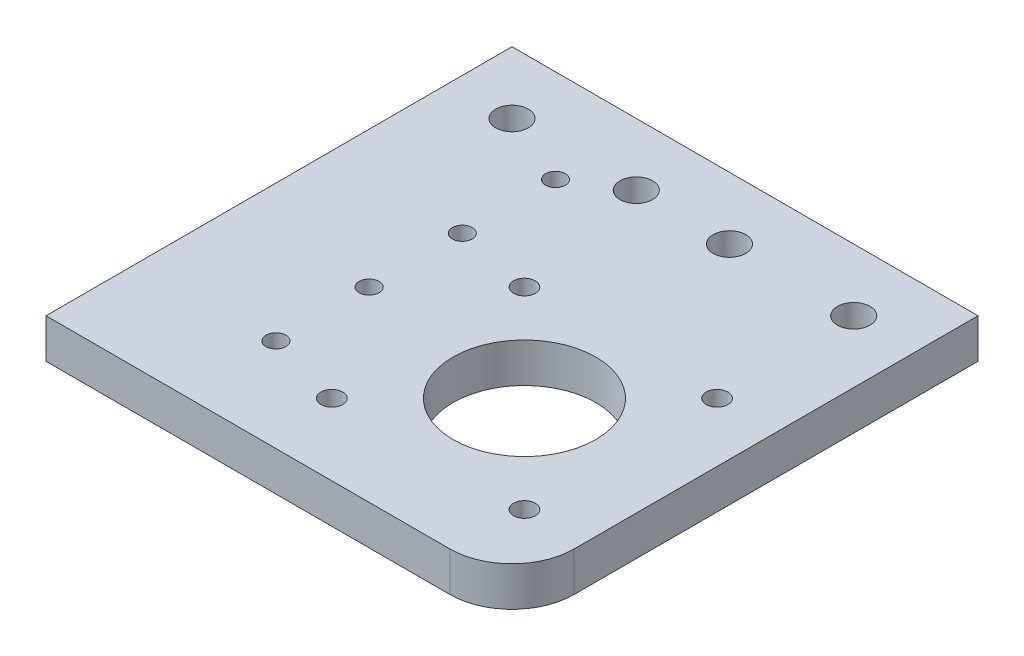
SolidWorks part; units mm, degrees
ref_plane "Front Plane" through (0, 0, 0) normal (0, 0, 1) x (1, 0, 0)
ref_plane "Top Plane" through (0, 0, 0) normal (0, 1, 0) x (1, 0, 0)
ref_plane "Right Plane" through (0, 0, 0) normal (1, 0, 0) x (0, 0, -1)
sketch "Sketch1" plane through (0, 0, 0) normal (0, 1, 0) x (1, 0, 0)
  line L0 (0, -10) -> (75, -10) construction
  line L1 (0, 0) -> (75, 0)
  line L2 (0, 0) -> (0, -75)
  line L3 (0, -75) -> (75, -75)
  line L4 (75, 0) -> (75, -75)
  circle A0 centre (10, -10) radius 2.625
  circle A1 centre (45, -10) radius 2.625
  circle A2 centre (65, -10) radius 2.625
  circle A3 centre (30, -10) radius 2.625
  dimension "D4" = 5.25
  dimension "D5" = 10
  dimension "D8" = 5.25
  dimension "D9" = 20
  dimension "D1" = 10
  dimension "D2" = 75
  dimension "D3" = 75
  dimension "D6" = 20
  dimension "D7" = 35
extrude "Boss-Extrude1" add sketch "Sketch1" along normal blind 6.35
fillet "Fillet1" radius 10 1 edges at (75, 3.175, 75)
sketch "Sketch3" plane through (0, 6.35, 0) normal (0, 1, 0) x (1, 0, 0)
  line L0 (34.5, -32.5) -> (65.5, -32.5) construction
  line L1 (34.5, -32.5) -> (34.5, -63.5) construction
  line L2 (65.5, -32.5) -> (65.5, -63.5) construction
  line L3 (34.5, -63.5) -> (65.5, -63.5) construction
  line L4 (34.5, -32.5) -> (65.5, -63.5) construction
  line L5 (75, -65) -> (75, 0) construction
  line L6 (55, 0) -> (55, -25) construction
  line L7 (75, 0) -> (0, 0) construction
  line L8 (55, -25) -> (75, -25) construction
  line L9 (28.5, -26.5) -> (71.5, -26.5) construction
  line L10 (28.5, -26.5) -> (28.5, -69.5) construction
  line L11 (71.5, -26.5) -> (71.5, -69.5) construction
  line L12 (28.5, -69.5) -> (71.5, -69.5) construction
  line L13 (28.5, -69.5) -> (71.5, -26.5) construction
  circle A0 centre (50, -48) radius 11.5
  circle A1 centre (34.5, -32.5) radius 1.75
  circle A2 centre (65.5, -32.5) radius 1.75
  circle A3 centre (65.5, -63.5) radius 1.75
  circle A4 centre (34.5, -63.5) radius 1.75
  dimension "D1" = 3.5
  dimension "D3" = 23
  dimension "D2" = 31
  dimension "D4" = 25
  dimension "D5" = 20
  dimension "D6" = 25
  dimension "D7" = 43
  dimension "D8" = 23
extrude "Cut-Extrude2" cut sketch "Sketch3" against normal through all
sketch "Sketch4" plane through (0, 6.35, 0) normal (0, 1, 0) x (1, 0, 0)
  line L0 (22, -15) -> (22, -30) construction
  line L3 (22, -30) -> (22, -45) construction
  line L4 (22, -45) -> (22, -60) construction
  line L5 (75, 0) -> (0, 0) construction
  circle A0 centre (22, -15) radius 1.6
  circle A1 centre (22, -30) radius 1.6
  circle A2 centre (22, -45) radius 1.6
  circle A3 centre (22, -60) radius 1.6
  circle A4 centre (34.5, -32.5) radius 1.75 construction
  dimension "D2" = 3.2
  dimension "D4" = 15
  dimension "D1" = 15
  dimension "D3" = 12.5
extrude "Cut-Extrude3" cut sketch "Sketch4" against normal through all
